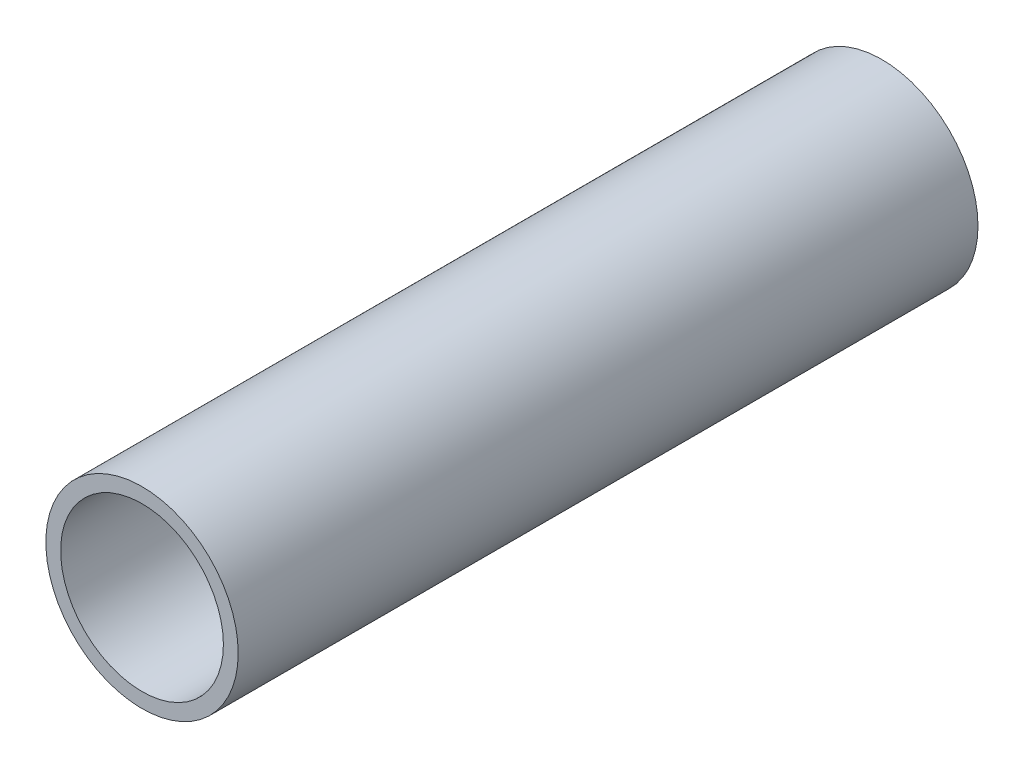
SolidWorks part; units mm, degrees
ref_plane "Front" through (0, 0, 0) normal (0, 0, 1) x (1, 0, 0)
ref_plane "Top" through (0, 0, 0) normal (0, 1, 0) x (1, 0, 0)
ref_plane "Right" through (0, 0, 0) normal (1, 0, 0) x (0, 0, -1)
sketch "Эскиз1" plane through (0, 0, 0) normal (0, 0, 1) x (1, 0, 0)
  circle A0 centre (0, 0) radius 55
  circle A1 centre (0, 0) radius 65
  dimension "D1" = 130
  dimension "D2" = 110
extrude "Бобышка-Вытянуть1" add sketch "Эскиз1" along normal blind 500
